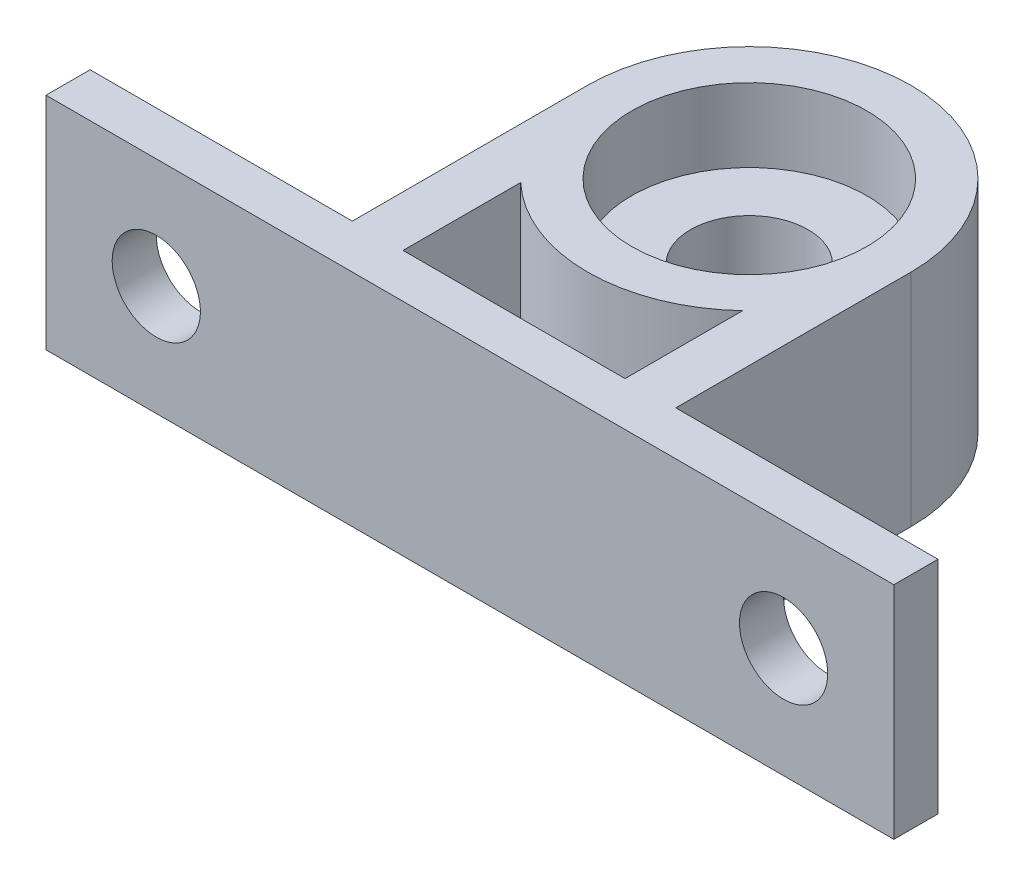
SolidWorks part; units mm, degrees
ref_plane "Front Plane" through (0, 0, 0) normal (0, 0, 1) x (1, 0, 0)
ref_plane "Top Plane" through (0, 0, 0) normal (0, 1, 0) x (1, 0, 0)
ref_plane "Right Plane" through (0, 0, 0) normal (1, 0, 0) x (0, 0, -1)
sketch "Sketch1" plane through (0, 0, 0) normal (0, 1, 0) x (1, 0, 0)
  line L1 (-28.8339, 15) -> (28.8339, 15)
  line L2 (-28.8339, 15) -> (-28.8339, -15)
  line L3 (-28.8339, -15) -> (28.8339, -15)
  line L4 (28.8339, 15) -> (28.8339, -15)
  line L5 (-28.8339, 15) -> (28.8339, -15) construction
  line L6 (-28.8339, -15) -> (28.8339, 15) construction
  point P0 (0, 0)
  dimension "D1" = 30
extrude "Boss-Extrude1" add sketch "Sketch1" along normal blind 15
sketch "Sketch2" plane through (0, 15, 0) normal (0, 1, 0) x (1, 0, 0)
  circle A0 centre (0, 4) radius 4
  dimension "D1" = 8
extrude "Cut-Extrude2" cut sketch "Sketch2" against normal blind 40
sketch "Sketch3" plane through (0, 15, 0) normal (0, 1, 0) x (1, 0, 0)
  circle A0 centre (0, 4) radius 8
  dimension "D1" = 16
extrude "Cut-Extrude3" cut sketch "Sketch3" against normal blind 5
sketch "Sketch4" plane through (0, 15, 0) normal (0, 1, 0) x (1, 0, 0)
  line L0 (11, 4) -> (11, -12)
  line L1 (11, -12) -> (28.8339, -12)
  line L2 (28.8339, -15) -> (28.8339, 15) construction
  line L3 (28.8339, -12) -> (28.8339, -15)
  line L4 (28.8339, -15) -> (-28.8339, -15)
  line L5 (-28.8339, -15) -> (-28.8339, -12)
  line L6 (-28.8339, 15) -> (-28.8339, -15) construction
  line L7 (-28.8339, -12) -> (-11, -12)
  line L8 (-11, -12) -> (-11, 4)
  line L9 (-28.8339, -12) -> (-28.8339, 15)
  line L10 (-28.8339, 15) -> (28.8339, 15)
  line L11 (28.8339, 15) -> (28.8339, -12)
  line L12 (-7.5498, -4) -> (-7.5498, -12)
  line L13 (-7.5498, -12) -> (7.5498, -12)
  line L14 (7.5498, -12) -> (7.5498, -4)
  circle A0 centre (0, 4) radius 11
  line M6 (28.8339, -15) -> (28.8339, 15)
  line M7 (28.8339, 15) -> (-28.8339, 15)
  line M8 (-28.8339, 15) -> (-28.8339, -15)
  dimension "D5" = 22
  dimension "D1" = 3
  dimension "D2" = 3
  dimension "D3" = 8
  dimension "D4" = 8
extrude "Cut-Extrude5" cut sketch "Sketch4" against normal through all contours A0 L10 L7 L8 M8 | A0 L0 L1 M6 M7 | A0 L12 L13 L14
sketch "Sketch5" plane through (0, 0, 12) normal (0, 0, -1) x (-1, 0, 0)
  line L0 (28.8339, 0) -> (11, 0) construction
  line L1 (28.8339, 0) -> (28.8339, 15) construction
  line L2 (-28.8339, 0) -> (-28.8339, 15) construction
  circle A0 centre (21.3339, 7.5) radius 3
  circle A1 centre (-21.3339, 7.5) radius 3
  dimension "D1" = 6
  dimension "D2" = 6
  dimension "D3" = 7.5
  dimension "D4" = 7.5
  dimension "D5" = 7.5
extrude "Cut-Extrude6" cut sketch "Sketch5" against normal blind 5
